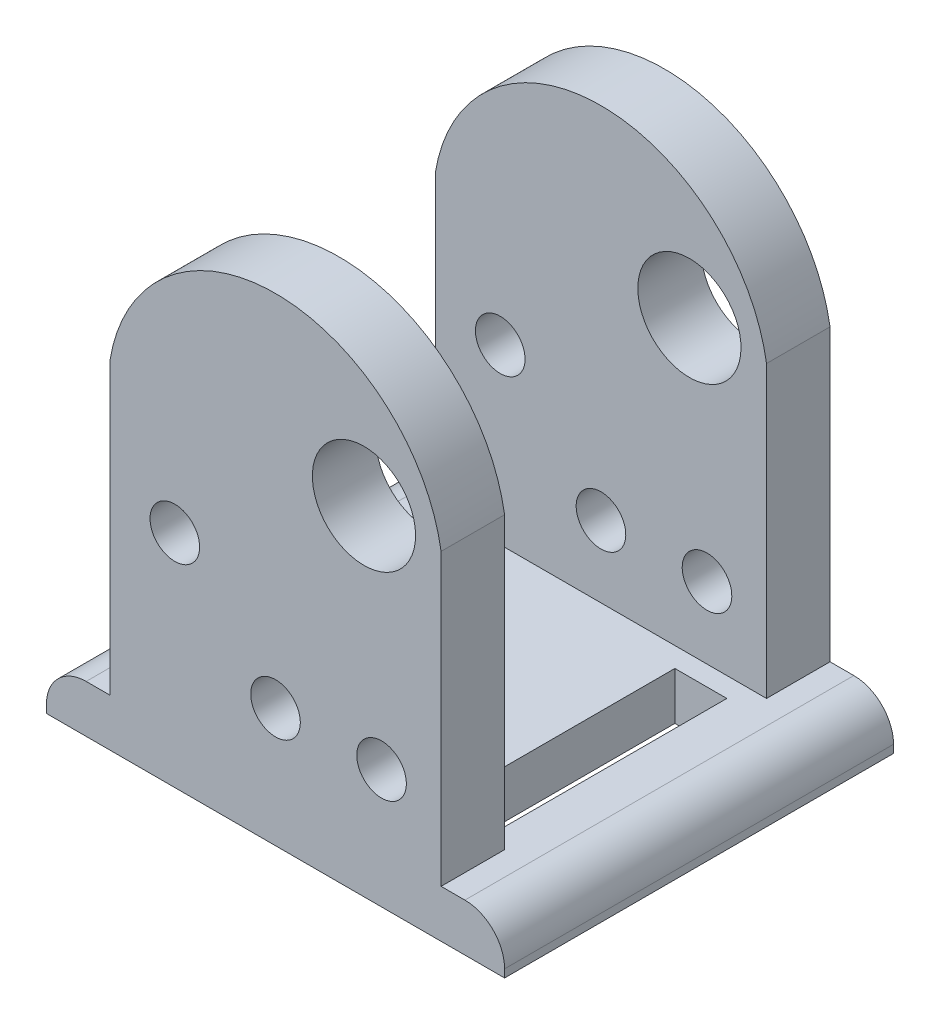
SolidWorks part; units mm, degrees
material "ABS"
ref_plane "Front Plane" through (0, 0, 0) normal (0, 0, 1) x (1, 0, 0)
ref_plane "Top Plane" through (0, 0, 0) normal (0, 1, 0) x (1, 0, 0)
ref_plane "Right Plane" through (0, 0, 0) normal (1, 0, 0) x (0, 0, -1)
sketch "Sketch2" plane through (0, 0, 0) normal (0, 0, 1) x (1, 0, 0)
  line L0 (4.5965, -0.056) -> (-20.6594, -0.056) construction
  line L1 (-20.6595, -21.67) -> (-20.6595, -26.8933) construction
  line L2 (8.6605, -21.67) -> (-20.6595, -21.67)
  line L3 (-16.5955, -7.5467) -> (4.5965, -7.5467) construction
  line L4 (-5.9995, -21.67) -> (-5.9995, 15.7549) construction
  line L5 (-0.3395, 8.9441) -> (-20.32, 8.9441) construction
  line L6 (-20.6595, -21.67) -> (-20.6595, -18.622)
  line L7 (8.6605, -21.67) -> (8.6605, -18.622)
  line L8 (-20.6595, -18.622) -> (-16.5955, -18.622)
  line L9 (-16.5955, -18.622) -> (-16.5955, -0.056)
  line L10 (8.6605, -18.622) -> (4.5965, -18.622)
  line L11 (4.5965, -18.622) -> (4.5965, -0.056)
  line L12 (-44.4945, 0) -> (34.7822, 0) construction
  line L13 (-0.3395, 0) -> (-0.3395, 26.7345) construction
  line L14 (0.7865, -14.05) -> (-13.1733, -14.05) construction
  circle A0 centre (-12.446, -7.5467) radius 1.5875
  arc A1 (-20.6594, -0.056) -> (8.6947, 0) centre (-5.968, -7.5467) cw construction
  circle A2 centre (-0.3395, 0) radius 3.302
  arc A3 (-16.5955, -0.056) -> (4.5965, -0.056) centre (-5.9995, -1.7935) cw
  circle A4 centre (-5.9995, -14.05) radius 1.5875
  circle A5 centre (0.7865, -14.05) radius 1.5875
  point P15 (-5.9995, 8.9441)
  point P26 (-16.5955, -0.056)
  dimension "D4" = 6.604
  dimension "D7" = 3.175
  dimension "D12" = 4.936
  dimension "D13" = 21.67
  dimension "D14" = 10.7375
  dimension "D15" = 3.175
  dimension "1/8in" = 3.175
  dimension "D1" = 20.32
  dimension "D2" = 4.064
  dimension "D3" = 3.048
  dimension "D8" = 3.81
  dimension "D9" = 7.62
  dimension "D10" = 21.67
  dimension "D11" = 29.32
extrude "Boss-Extrude1" add sketch "Sketch2" along normal blind 24.892 contours L9 A3 L11 L10 L7 L2 L6 L8
sketch "Sketch3" plane through (-16.5955, 0, 0) normal (-1, 0, 0) x (0, 0, 1)
  line L0 (20.828, -18.622) -> (20.828, 11.1955)
  line L1 (24.892, -0.056) -> (0, -0.056) construction
  line L2 (0, -0.056) -> (0, -18.622) construction
  line L3 (4.064, -0.056) -> (4.064, -18.622)
  line L4 (24.892, -18.622) -> (0, -18.622) construction
  line L5 (4.064, -18.622) -> (20.828, -18.622)
  line L6 (24.892, -18.622) -> (0, -18.622) construction
  line L9 (4.064, -0.056) -> (4.064, 11.1955)
  line L10 (4.064, 11.1955) -> (20.828, 11.1955)
  dimension "D1" = 16.764
  dimension "D2" = 4.064
  dimension "D3" = 29.8175
extrude "Cut-Extrude2" cut sketch "Sketch3" against normal blind 21.844 contours L10 L0 L5 L3 L9
sketch "Sketch4" plane through (0, -18.622, 0) normal (0, 1, 0) x (1, 0, 0)
  line L0 (4.5965, -4.064) -> (-16.5955, -4.064) construction
  line L1 (4.5965, -20.828) -> (-16.5955, -20.828) construction
  line L2 (4.5965, -4.064) -> (-16.5955, -4.064) construction
  line L3 (4.5965, -20.828) -> (-16.5955, -20.828) construction
  line L4 (-16.5955, -20.828) -> (-16.5955, -4.064) construction
  line L5 (4.5965, -20.828) -> (4.5965, -4.064) construction
  line L6 (3.3265, -5.334) -> (0, -5.334)
  line L7 (-15.3255, -19.558) -> (-15.3255, -5.334)
  line L8 (3.3265, -19.558) -> (0, -19.558)
  line L9 (3.3265, -19.558) -> (3.3265, -5.334)
  line L10 (-11.5155, -5.334) -> (-11.5155, -19.558)
  line L11 (0, -5.334) -> (0, -19.558)
  line L12 (-11.5155, -5.334) -> (-15.3255, -5.334)
  line L13 (3.3265, -5.334) -> (-15.3255, -5.334) construction
  line L14 (-11.5155, -19.558) -> (-15.3255, -19.558)
  line L15 (3.3265, -19.558) -> (-15.3255, -19.558) construction
  dimension "D2" = 3.81
  dimension "D1" = 1.27
extrude "Cut-Extrude3" cut sketch "Sketch4" against normal blind 21.844 contours L6 L11 L8 L9 | L10 L14 L7 L12
fillet "Fillet1" radius 2.54 2 edges at (8.6605, -18.622, 12.446) (-20.6595, -18.622, 12.446)
